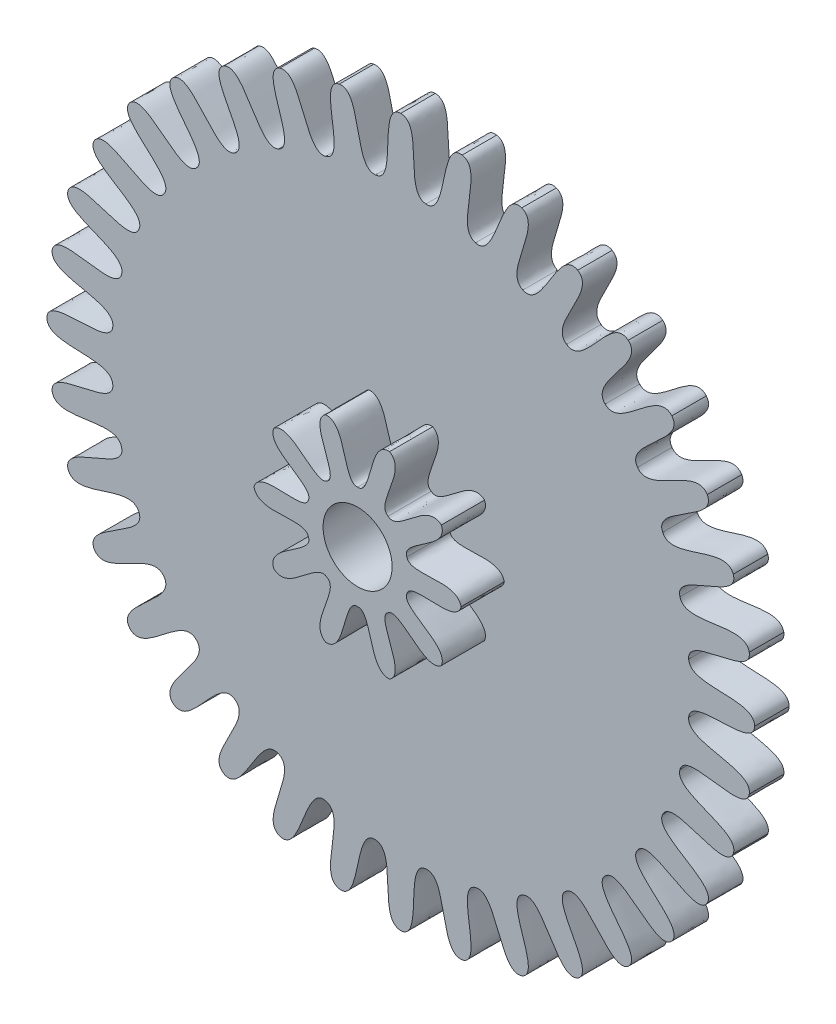
SolidWorks part; units mm, degrees
ref_plane "Alzado" through (0, 0, 0) normal (0, 0, 1) x (1, 0, 0)
ref_plane "Planta" through (0, 0, 0) normal (0, 1, 0) x (1, 0, 0)
ref_plane "Vista lateral" through (0, 0, 0) normal (1, 0, 0) x (0, 0, -1)
sketch "Sketch1" plane through (0, 0, 0) normal (0, 0, 1) x (1, 0, 0)
  line L0 (0, -1000) -> (0, 49000) construction
  line L1 (0, 0) -> (4357.7871, 49809.7349) construction
  line L2 (0, 0) -> (-4357.7871, 49809.7349) construction
  circle A0 centre (0, 0) radius 4.1 construction
  circle A1 centre (0, 0) radius 3.35 construction
  spline S0 degree 3 poles (0, 4.1) (0.2702, 4.0938) (0.032, 3.3537) (0.2919, 3.3362) knots 0 0 0 0 1 1 1 1
  spline S1 degree 3 poles (0, 4.1) (-0.2702, 4.0938) (-0.032, 3.3537) (-0.2919, 3.3362) knots 0 0 0 0 1 1 1 1
  spline S2 degree 3 poles (0.712, 4.0377) (0.4447, 4.0785) (0.5508, 3.3083) (0.2919, 3.3362) knots 0 0 0 0 1 1 1 1
  spline S3 degree 3 poles (0.712, 4.0377) (0.977, 3.9846) (0.6139, 3.2972) (0.8668, 3.2348) knots 0 0 0 0 1 1 1 1
  spline S4 degree 3 poles (1.4023, 3.8527) (1.1462, 3.9393) (1.1169, 3.1624) (0.8668, 3.2348) knots 0 0 0 0 1 1 1 1
  spline S5 degree 3 poles (1.4023, 3.8527) (1.6541, 3.7544) (1.1771, 3.1405) (1.4153, 3.0352) knots 0 0 0 0 1 1 1 1
  spline S6 degree 3 poles (2.05, 3.5507) (1.8128, 3.6804) (1.6491, 2.9204) (1.4153, 3.0352) knots 0 0 0 0 1 1 1 1
  spline S7 degree 3 poles (2.05, 3.5507) (2.2809, 3.4102) (1.7046, 2.8884) (1.9209, 2.7433) knots 0 0 0 0 1 1 1 1
  spline S8 degree 3 poles (2.6354, 3.1408) (2.4244, 3.3097) (2.1312, 2.5896) (1.9209, 2.7433) knots 0 0 0 0 1 1 1 1
  spline S9 degree 3 poles (2.6354, 3.1408) (2.8384, 2.9623) (2.1802, 2.5485) (2.3681, 2.3681) knots 0 0 0 0 1 1 1 1
  spline S10 degree 3 poles (3.1408, 2.6354) (2.9623, 2.8384) (2.5485, 2.1802) (2.3681, 2.3681) knots 0 0 0 0 1 1 1 1
  spline S11 degree 3 poles (3.1408, 2.6354) (3.3097, 2.4244) (2.5896, 2.1312) (2.7433, 1.9209) knots 0 0 0 0 1 1 1 1
  spline S12 degree 3 poles (3.5507, 2.05) (3.4102, 2.2809) (2.8884, 1.7046) (2.7433, 1.9209) knots 0 0 0 0 1 1 1 1
  spline S13 degree 3 poles (3.5507, 2.05) (3.6804, 1.8128) (2.9204, 1.6491) (3.0352, 1.4153) knots 0 0 0 0 1 1 1 1
  spline S14 degree 3 poles (3.8527, 1.4023) (3.7544, 1.6541) (3.1405, 1.1771) (3.0352, 1.4153) knots 0 0 0 0 1 1 1 1
  spline S15 degree 3 poles (3.8527, 1.4023) (3.9393, 1.1462) (3.1624, 1.1169) (3.2348, 0.8668) knots 0 0 0 0 1 1 1 1
  spline S16 degree 3 poles (4.0377, 0.712) (3.9846, 0.977) (3.2972, 0.6139) (3.2348, 0.8668) knots 0 0 0 0 1 1 1 1
  spline S17 degree 3 poles (4.0377, 0.712) (4.0785, 0.4447) (3.3083, 0.5508) (3.3362, 0.2919) knots 0 0 0 0 1 1 1 1
  spline S18 degree 3 poles (4.1, 0) (4.0938, 0.2702) (3.3537, 0.032) (3.3362, 0.2919) knots 0 0 0 0 1 1 1 1
  spline S19 degree 3 poles (4.1, 0) (4.0938, -0.2702) (3.3537, -0.032) (3.3362, -0.2919) knots 0 0 0 0 1 1 1 1
  spline S20 degree 3 poles (4.0377, -0.712) (4.0785, -0.4447) (3.3083, -0.5508) (3.3362, -0.2919) knots 0 0 0 0 1 1 1 1
  spline S21 degree 3 poles (4.0377, -0.712) (3.9846, -0.977) (3.2972, -0.6139) (3.2348, -0.8668) knots 0 0 0 0 1 1 1 1
  spline S22 degree 3 poles (3.8527, -1.4023) (3.9393, -1.1462) (3.1624, -1.1169) (3.2348, -0.8668) knots 0 0 0 0 1 1 1 1
  spline S23 degree 3 poles (3.8527, -1.4023) (3.7544, -1.6541) (3.1405, -1.1771) (3.0352, -1.4153) knots 0 0 0 0 1 1 1 1
  spline S24 degree 3 poles (3.5507, -2.05) (3.6804, -1.8128) (2.9204, -1.6491) (3.0352, -1.4153) knots 0 0 0 0 1 1 1 1
  spline S25 degree 3 poles (3.5507, -2.05) (3.4102, -2.2809) (2.8884, -1.7046) (2.7433, -1.9209) knots 0 0 0 0 1 1 1 1
  spline S26 degree 3 poles (3.1408, -2.6354) (3.3097, -2.4244) (2.5896, -2.1312) (2.7433, -1.9209) knots 0 0 0 0 1 1 1 1
  spline S27 degree 3 poles (3.1408, -2.6354) (2.9623, -2.8384) (2.5485, -2.1802) (2.3681, -2.3681) knots 0 0 0 0 1 1 1 1
  spline S28 degree 3 poles (2.6354, -3.1408) (2.8384, -2.9623) (2.1802, -2.5485) (2.3681, -2.3681) knots 0 0 0 0 1 1 1 1
  spline S29 degree 3 poles (2.6354, -3.1408) (2.4244, -3.3097) (2.1312, -2.5896) (1.9209, -2.7433) knots 0 0 0 0 1 1 1 1
  spline S30 degree 3 poles (2.05, -3.5507) (2.2809, -3.4102) (1.7046, -2.8884) (1.9209, -2.7433) knots 0 0 0 0 1 1 1 1
  spline S31 degree 3 poles (2.05, -3.5507) (1.8128, -3.6804) (1.6491, -2.9204) (1.4153, -3.0352) knots 0 0 0 0 1 1 1 1
  spline S32 degree 3 poles (1.4023, -3.8527) (1.6541, -3.7544) (1.1771, -3.1405) (1.4153, -3.0352) knots 0 0 0 0 1 1 1 1
  spline S33 degree 3 poles (1.4023, -3.8527) (1.1462, -3.9393) (1.1169, -3.1624) (0.8668, -3.2348) knots 0 0 0 0 1 1 1 1
  spline S34 degree 3 poles (0.712, -4.0377) (0.977, -3.9846) (0.6139, -3.2972) (0.8668, -3.2348) knots 0 0 0 0 1 1 1 1
  spline S35 degree 3 poles (0.712, -4.0377) (0.4447, -4.0785) (0.5508, -3.3083) (0.2919, -3.3362) knots 0 0 0 0 1 1 1 1
  spline S36 degree 3 poles (0, -4.1) (0.2702, -4.0938) (0.032, -3.3537) (0.2919, -3.3362) knots 0 0 0 0 1 1 1 1
  spline S37 degree 3 poles (0, -4.1) (-0.2702, -4.0938) (-0.032, -3.3537) (-0.2919, -3.3362) knots 0 0 0 0 1 1 1 1
  spline S38 degree 3 poles (-0.712, -4.0377) (-0.4447, -4.0785) (-0.5508, -3.3083) (-0.2919, -3.3362) knots 0 0 0 0 1 1 1 1
  spline S39 degree 3 poles (-0.712, -4.0377) (-0.977, -3.9846) (-0.6139, -3.2972) (-0.8668, -3.2348) knots 0 0 0 0 1 1 1 1
  spline S40 degree 3 poles (-1.4023, -3.8527) (-1.1462, -3.9393) (-1.1169, -3.1624) (-0.8668, -3.2348) knots 0 0 0 0 1 1 1 1
  spline S41 degree 3 poles (-1.4023, -3.8527) (-1.6541, -3.7544) (-1.1771, -3.1405) (-1.4153, -3.0352) knots 0 0 0 0 1 1 1 1
  spline S42 degree 3 poles (-2.05, -3.5507) (-1.8128, -3.6804) (-1.6491, -2.9204) (-1.4153, -3.0352) knots 0 0 0 0 1 1 1 1
  spline S43 degree 3 poles (-2.05, -3.5507) (-2.2809, -3.4102) (-1.7046, -2.8884) (-1.9209, -2.7433) knots 0 0 0 0 1 1 1 1
  spline S44 degree 3 poles (-2.6354, -3.1408) (-2.4244, -3.3097) (-2.1312, -2.5896) (-1.9209, -2.7433) knots 0 0 0 0 1 1 1 1
  spline S45 degree 3 poles (-2.6354, -3.1408) (-2.8384, -2.9623) (-2.1802, -2.5485) (-2.3681, -2.3681) knots 0 0 0 0 1 1 1 1
  spline S46 degree 3 poles (-3.1408, -2.6354) (-2.9623, -2.8384) (-2.5485, -2.1802) (-2.3681, -2.3681) knots 0 0 0 0 1 1 1 1
  spline S47 degree 3 poles (-3.1408, -2.6354) (-3.3097, -2.4244) (-2.5896, -2.1312) (-2.7433, -1.9209) knots 0 0 0 0 1 1 1 1
  spline S48 degree 3 poles (-3.5507, -2.05) (-3.4102, -2.2809) (-2.8884, -1.7046) (-2.7433, -1.9209) knots 0 0 0 0 1 1 1 1
  spline S49 degree 3 poles (-3.5507, -2.05) (-3.6804, -1.8128) (-2.9204, -1.6491) (-3.0352, -1.4153) knots 0 0 0 0 1 1 1 1
  spline S50 degree 3 poles (-3.8527, -1.4023) (-3.7544, -1.6541) (-3.1405, -1.1771) (-3.0352, -1.4153) knots 0 0 0 0 1 1 1 1
  spline S51 degree 3 poles (-3.8527, -1.4023) (-3.9393, -1.1462) (-3.1624, -1.1169) (-3.2348, -0.8668) knots 0 0 0 0 1 1 1 1
  spline S52 degree 3 poles (-4.0377, -0.712) (-3.9846, -0.977) (-3.2972, -0.6139) (-3.2348, -0.8668) knots 0 0 0 0 1 1 1 1
  spline S53 degree 3 poles (-4.0377, -0.712) (-4.0785, -0.4447) (-3.3083, -0.5508) (-3.3362, -0.2919) knots 0 0 0 0 1 1 1 1
  spline S54 degree 3 poles (-4.1, 0) (-4.0938, -0.2702) (-3.3537, -0.032) (-3.3362, -0.2919) knots 0 0 0 0 1 1 1 1
  spline S55 degree 3 poles (-4.1, 0) (-4.0938, 0.2702) (-3.3537, 0.032) (-3.3362, 0.2919) knots 0 0 0 0 1 1 1 1
  spline S56 degree 3 poles (-4.0377, 0.712) (-4.0785, 0.4447) (-3.3083, 0.5508) (-3.3362, 0.2919) knots 0 0 0 0 1 1 1 1
  spline S57 degree 3 poles (-4.0377, 0.712) (-3.9846, 0.977) (-3.2972, 0.6139) (-3.2348, 0.8668) knots 0 0 0 0 1 1 1 1
  spline S58 degree 3 poles (-3.8527, 1.4023) (-3.9393, 1.1462) (-3.1624, 1.1169) (-3.2348, 0.8668) knots 0 0 0 0 1 1 1 1
  spline S59 degree 3 poles (-3.8527, 1.4023) (-3.7544, 1.6541) (-3.1405, 1.1771) (-3.0352, 1.4153) knots 0 0 0 0 1 1 1 1
  spline S60 degree 3 poles (-3.5507, 2.05) (-3.6804, 1.8128) (-2.9204, 1.6491) (-3.0352, 1.4153) knots 0 0 0 0 1 1 1 1
  spline S61 degree 3 poles (-3.5507, 2.05) (-3.4102, 2.2809) (-2.8884, 1.7046) (-2.7433, 1.9209) knots 0 0 0 0 1 1 1 1
  spline S62 degree 3 poles (-3.1408, 2.6354) (-3.3097, 2.4244) (-2.5896, 2.1312) (-2.7433, 1.9209) knots 0 0 0 0 1 1 1 1
  spline S63 degree 3 poles (-3.1408, 2.6354) (-2.9623, 2.8384) (-2.5485, 2.1802) (-2.3681, 2.3681) knots 0 0 0 0 1 1 1 1
  spline S64 degree 3 poles (-2.6354, 3.1408) (-2.8384, 2.9623) (-2.1802, 2.5485) (-2.3681, 2.3681) knots 0 0 0 0 1 1 1 1
  spline S65 degree 3 poles (-2.6354, 3.1408) (-2.4244, 3.3097) (-2.1312, 2.5896) (-1.9209, 2.7433) knots 0 0 0 0 1 1 1 1
  spline S66 degree 3 poles (-2.05, 3.5507) (-2.2809, 3.4102) (-1.7046, 2.8884) (-1.9209, 2.7433) knots 0 0 0 0 1 1 1 1
  spline S67 degree 3 poles (-2.05, 3.5507) (-1.8128, 3.6804) (-1.6491, 2.9204) (-1.4153, 3.0352) knots 0 0 0 0 1 1 1 1
  spline S68 degree 3 poles (-1.4023, 3.8527) (-1.6541, 3.7544) (-1.1771, 3.1405) (-1.4153, 3.0352) knots 0 0 0 0 1 1 1 1
  spline S69 degree 3 poles (-1.4023, 3.8527) (-1.1462, 3.9393) (-1.1169, 3.1624) (-0.8668, 3.2348) knots 0 0 0 0 1 1 1 1
  spline S70 degree 3 poles (-0.712, 4.0377) (-0.977, 3.9846) (-0.6139, 3.2972) (-0.8668, 3.2348) knots 0 0 0 0 1 1 1 1
  spline S71 degree 3 poles (-0.712, 4.0377) (-0.4447, 4.0785) (-0.5508, 3.3083) (-0.2919, 3.3362) knots 0 0 0 0 1 1 1 1
  point P4 (0, 4.1)
  point P11 (0.2919, 3.3362)
  point P122 (0, 0)
  dimension "D1" = 8.2
  dimension "D2" = 6.7
  dimension "D3" = 5
  dimension "D4" = 5
extrude "Boss-Extrude1 (36 teeth)" add sketch "Sketch1" along normal blind 0.4
sketch "Sketch2" plane through (0, 0, 0.4) normal (0, 0, 1) x (1, 0, 0)
  line L0 (0, -1000) -> (0, 49000) construction
  line L1 (0, 0) -> (15450.8497, 47552.8258) construction
  line L2 (0, 0) -> (29389.2626, 40450.8497) construction
  circle A0 centre (0, 0) radius 1.2 construction
  circle A1 centre (0, 0) radius 0.6 construction
  spline S0 degree 3 poles (0.3708, 1.1413) (0.5807, 1.0128) (0.2021, 0.5695) (0.3527, 0.4854) knots 0 0 0 0 1 1 1 1
  spline S1 degree 3 poles (0.3708, 1.1413) (0.1255, 1.1608) (0.1712, 0.5795) (0, 0.6) knots 0 0 0 0 1 1 1 1
  spline S2 degree 3 poles (0.9708, 0.7053) (0.7838, 0.8653) (0.4791, 0.3682) (0.3527, 0.4854) knots 0 0 0 0 1 1 1 1
  spline S3 degree 3 poles (0.9708, 0.7053) (1.0652, 0.4781) (0.4982, 0.3419) (0.5706, 0.1854) knots 0 0 0 0 1 1 1 1
  spline S4 degree 3 poles (1.2, 0) (1.1427, 0.2393) (0.6041, 0.0162) (0.5706, 0.1854) knots 0 0 0 0 1 1 1 1
  spline S5 degree 3 poles (1.2, 0) (1.1427, -0.2393) (0.6041, -0.0162) (0.5706, -0.1854) knots 0 0 0 0 1 1 1 1
  spline S6 degree 3 poles (0.9708, -0.7053) (1.0652, -0.4781) (0.4982, -0.3419) (0.5706, -0.1854) knots 0 0 0 0 1 1 1 1
  spline S7 degree 3 poles (0.9708, -0.7053) (0.7838, -0.8653) (0.4791, -0.3682) (0.3527, -0.4854) knots 0 0 0 0 1 1 1 1
  spline S8 degree 3 poles (0.3708, -1.1413) (0.5807, -1.0128) (0.2021, -0.5695) (0.3527, -0.4854) knots 0 0 0 0 1 1 1 1
  spline S9 degree 3 poles (0.3708, -1.1413) (0.1255, -1.1608) (0.1712, -0.5795) (0, -0.6) knots 0 0 0 0 1 1 1 1
  spline S10 degree 3 poles (-0.3708, -1.1413) (-0.1255, -1.1608) (-0.1712, -0.5795) (0, -0.6) knots 0 0 0 0 1 1 1 1
  spline S11 degree 3 poles (-0.3708, -1.1413) (-0.5807, -1.0128) (-0.2021, -0.5695) (-0.3527, -0.4854) knots 0 0 0 0 1 1 1 1
  spline S12 degree 3 poles (-0.9708, -0.7053) (-0.7838, -0.8653) (-0.4791, -0.3682) (-0.3527, -0.4854) knots 0 0 0 0 1 1 1 1
  spline S13 degree 3 poles (-0.9708, -0.7053) (-1.0652, -0.4781) (-0.4982, -0.3419) (-0.5706, -0.1854) knots 0 0 0 0 1 1 1 1
  spline S14 degree 3 poles (-1.2, 0) (-1.1427, -0.2393) (-0.6041, -0.0162) (-0.5706, -0.1854) knots 0 0 0 0 1 1 1 1
  spline S15 degree 3 poles (-1.2, 0) (-1.1427, 0.2393) (-0.6041, 0.0162) (-0.5706, 0.1854) knots 0 0 0 0 1 1 1 1
  spline S16 degree 3 poles (-0.9708, 0.7053) (-1.0652, 0.4781) (-0.4982, 0.3419) (-0.5706, 0.1854) knots 0 0 0 0 1 1 1 1
  spline S17 degree 3 poles (-0.9708, 0.7053) (-0.7838, 0.8653) (-0.4791, 0.3682) (-0.3527, 0.4854) knots 0 0 0 0 1 1 1 1
  spline S18 degree 3 poles (-0.3708, 1.1413) (-0.5807, 1.0128) (-0.2021, 0.5695) (-0.3527, 0.4854) knots 0 0 0 0 1 1 1 1
  spline S19 degree 3 poles (-0.3708, 1.1413) (-0.1255, 1.1608) (-0.1712, 0.5795) (0, 0.6) knots 0 0 0 0 1 1 1 1
  point P4 (0.3708, 1.1413)
  point P10 (0.3527, 0.4854)
  point P45 (0, 0)
  dimension "D1" = 2.4
  dimension "D2" = 1.2
  dimension "D3" = 18
  dimension "D4" = 18
extrude "Boss-Extrude2 (10 teeth)" add sketch "Sketch2" along normal blind 0.5
sketch "Sketch3" plane through (0, 0, 0) normal (0, 0, 1) x (1, 0, 0)
  circle A0 centre (0, 0) radius 0.4
  dimension "D1" = 0.8
extrude "Cut-Extrude1" cut sketch "Sketch3" along normal through all
